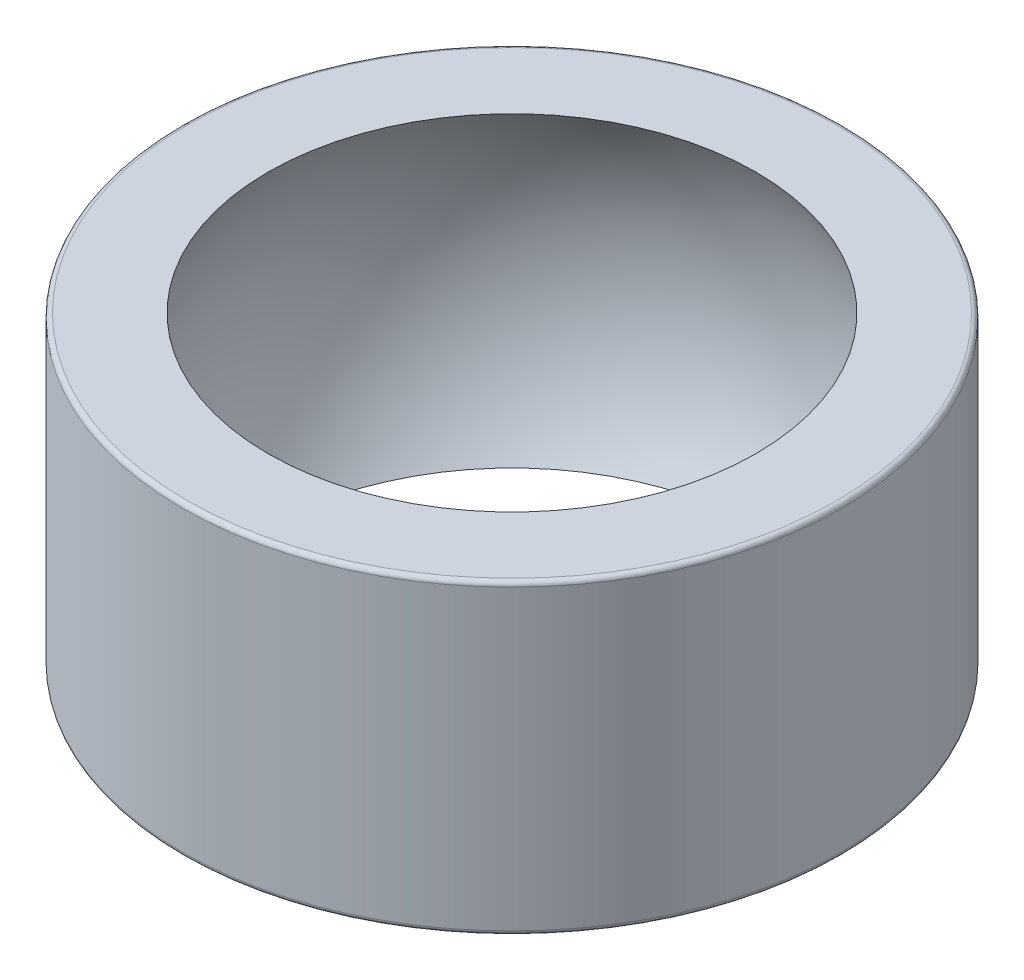
SolidWorks part; units mm, degrees
material "1.0545 (S355N)"
ref_plane "Płaszczyzna przednia" through (0, 0, 0) normal (0, 0, 1) x (1, 0, 0)
ref_plane "Płaszczyzna górna" through (0, 0, 0) normal (0, 1, 0) x (1, 0, 0)
ref_plane "Płaszczyzna prawa" through (0, 0, 0) normal (1, 0, 0) x (0, 0, -1)
sketch "Szkic1" plane through (0, 0, 0) normal (0, 1, 0) x (1, 0, 0)
  circle A0 centre (0, 0) radius 14.5
  dimension "d2" = 29
extrude "Dodanie-wyciągnięcie1" add sketch "Szkic1" along normal mid plane 13.5
sketch "Szkic3" plane through (0, 0, 0) normal (0, 0, 1) x (1, 0, 0)
  line L0 (0, -12.68) -> (0, 12.68)
  arc A0 (0, -12.68) -> (0, 12.68) centre (0, 0) ccw
  dimension "d3" = 25.36
revolve "Wycięcie-obrót1" cut sketch "Szkic3" angle 360 about L0
fillet "Zaokrąglenie1" radius 0.2 2 edges at (0, 6.75, 14.5) (0, -6.75, 14.5)
